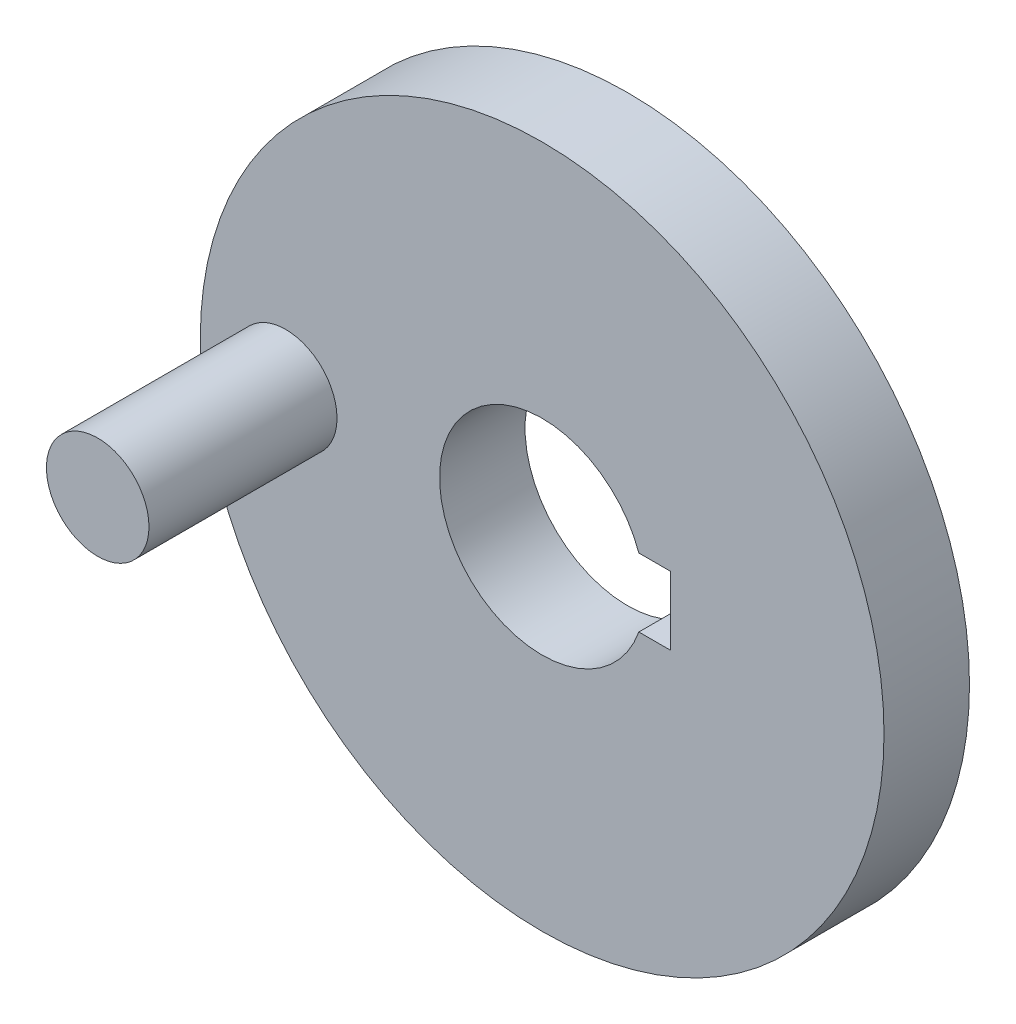
SolidWorks part; units mm, degrees
ref_plane "Front Plane" through (0, 0, 0) normal (0, 0, 1) x (1, 0, 0)
ref_plane "Top Plane" through (0, 0, 0) normal (0, 1, 0) x (1, 0, 0)
ref_plane "Right Plane" through (0, 0, 0) normal (1, 0, 0) x (0, 0, -1)
sketch "Sketch1" plane through (0, 0, 0) normal (0, 0, 1) x (1, 0, 0)
  circle A0 centre (0, 0) radius 20
extrude "Boss-Extrude1" add sketch "Sketch1" along normal blind 5
sketch "Sketch3" plane through (0, 0, 5) normal (0, 0, 1) x (1, 0, 0)
  circle A0 centre (-15, 0) radius 3
extrude "Boss-Extrude2" add sketch "Sketch3" along normal blind 11
sketch "Sketch5" plane through (0, 0, 5) normal (0, 0, 1) x (1, 0, 0)
  line L3 (5.6569, 2) -> (7.5, 2)
  line L4 (7.5, 2) -> (7.5, -2)
  line L5 (7.5, -2) -> (5.6569, -2)
  arc A0 (5.6569, 2) -> (5.6569, -2) centre (0, 0) ccw
extrude "Cut-Extrude1" cut sketch "Sketch5" against normal through all
